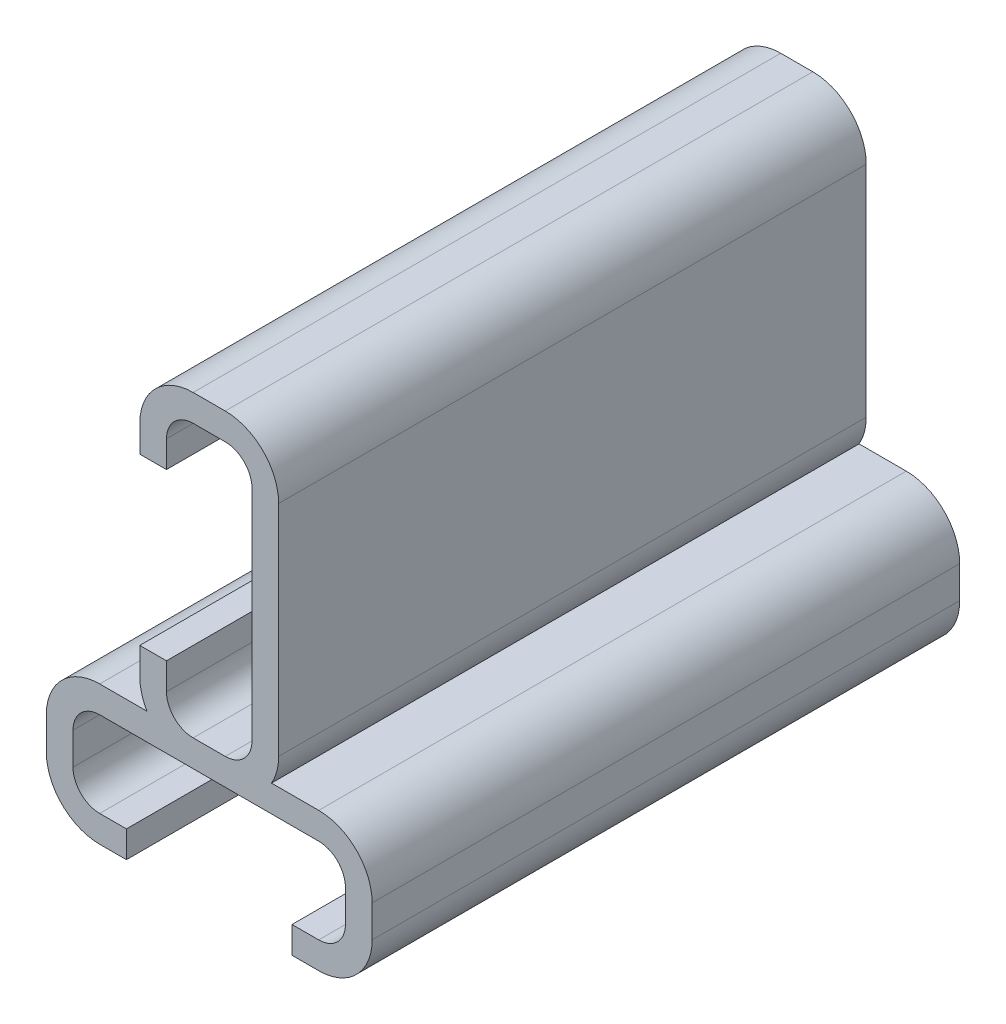
SolidWorks part; units mm, degrees
ref_plane "Plan de face" through (0, 0, 0) normal (0, 0, 1) x (1, 0, 0)
ref_plane "Plan de dessus" through (0, 0, 0) normal (0, 1, 0) x (1, 0, 0)
ref_plane "Plan de droite" through (0, 0, 0) normal (1, 0, 0) x (0, 0, -1)
sketch "Esquisse1" plane through (0, 0, 0) normal (0, 0, 1) x (1, 0, 0)
  line L1 (5.1, 0.6) -> (5.1, -0.6)
  line L2 (4.1, -1.6) -> (-4.1, -1.6)
  line L3 (-5.1, -0.6) -> (-5.1, 0.6)
  line L5 (6.1, 0.6) -> (6.1, -0.6)
  line L6 (4.1, -2.6) -> (-4.1, -2.6)
  line L7 (-6.1, -0.6) -> (-6.1, 0.6)
  line L8 (2.6, 3.6) -> (2.6, 11.8)
  line L9 (-0.6, 2.6) -> (0.6, 2.6)
  line L10 (-1.6, 3.6) -> (-1.6, 11.8)
  line L11 (-0.6, 12.8) -> (0.6, 12.8)
  line L12 (1.6, 3.6) -> (1.6, 11.8)
  line L13 (-0.6, 13.8) -> (0.6, 13.8)
  line L14 (-2.6, 3.6) -> (-2.6, 11.8)
  line L16 (-4.1, 2.6) -> (4.1, 2.6) construction
  line L17 (4.1, 2.6) -> (2.3321, 2.6)
  line L18 (-4.1, 2.6) -> (-2.3321, 2.6)
  line L19 (-4.1, 1.6) -> (4.1, 1.6)
  line L20 (-4.1, 1.6) -> (4.1, 1.6) construction
  line L21 (-0.6, 1.6) -> (0.6, 1.6) construction
  arc A0 (-4.1, -1.6) -> (-5.1, -0.6) centre (-4.1, -0.6) cw
  arc A1 (5.1, -0.6) -> (4.1, -1.6) centre (4.1, -0.6) cw
  arc A2 (4.1, 1.6) -> (5.1, 0.6) centre (4.1, 0.6) cw
  arc A3 (-4.1, 1.6) -> (-5.1, 0.6) centre (-4.1, 0.6) ccw
  arc A4 (4.1, 2.6) -> (6.1, 0.6) centre (4.1, 0.6) cw
  arc A5 (6.1, -0.6) -> (4.1, -2.6) centre (4.1, -0.6) cw
  arc A6 (-4.1, -2.6) -> (-6.1, -0.6) centre (-4.1, -0.6) cw
  arc A7 (-4.1, 2.6) -> (-6.1, 0.6) centre (-4.1, 0.6) ccw
  arc A8 (0.6, 2.6) -> (1.6, 3.6) centre (0.6, 3.6) ccw
  arc A9 (-0.6, 2.6) -> (-1.6, 3.6) centre (-0.6, 3.6) cw
  arc A10 (-1.6, 11.8) -> (-0.6, 12.8) centre (-0.6, 11.8) cw
  arc A11 (0.6, 12.8) -> (1.6, 11.8) centre (0.6, 11.8) cw
  arc A12 (0.6, 13.8) -> (2.6, 11.8) centre (0.6, 11.8) cw
  arc A13 (-2.6, 11.8) -> (-0.6, 13.8) centre (-0.6, 11.8) cw
  arc A14 (-0.6, 1.6) -> (-2.6, 3.6) centre (-0.6, 3.6) cw construction
  arc A15 (0.6, 1.6) -> (2.6, 3.6) centre (0.6, 3.6) ccw construction
  arc A16 (2.6, 3.6) -> (2.3321, 2.6) centre (0.6, 3.6) cw
  arc A17 (-2.6, 3.6) -> (-2.3321, 2.6) centre (-0.6, 3.6) ccw
  point P6 (-5.1, -1.6)
  point P11 (5.1, 1.6)
  point P14 (-5.1, 1.6)
  point P15 (0, 1.6)
  point P16 (-5.1, 0)
  point P37 (1.6, 2.6)
  point P40 (-1.6, 2.6)
  point P43 (-1.6, 12.8)
  point P46 (1.6, 12.8)
  point P63 (0, 2.6)
  dimension "D3" = 1
  dimension "D7" = 1
  dimension "D1" = 3.2
  dimension "D2" = 10.2
  dimension "D5" = 3.2
  dimension "D6" = 10.2
  dimension "D9" = 3.2
  dimension "D4" = 1
  dimension "D8" = 1
extrude "Boss.-Extru.2" add sketch "Esquisse1" along normal blind 10 contours L17 A16 L8 A12 L13 A13 L14 A17 L18 A7 L7 A6 L6 A5 L5 A4 | L10 A10 L11 A11 L12 A8 L9 A9 | L19 A2 L1 A1 L2 A0 L3 A3
sketch "Esquisse7" plane through (0, 0, 0) normal (0, 0, -1) x (-1, 0, 0)
  line L8 (-6.1, 0.6) -> (-6.1, -0.6)
  line L9 (-4.1, -2.6) -> (4.1, -2.6)
  line L10 (6.1, -0.6) -> (6.1, 0.6)
  line L11 (4.1, 2.6) -> (2.3321, 2.6)
  line L12 (2.6, 3.6) -> (2.6, 11.8)
  line L13 (0.6, 13.8) -> (-0.6, 13.8)
  line L14 (-2.6, 11.8) -> (-2.6, 3.6)
  line L15 (-2.3321, 2.6) -> (-4.1, 2.6)
  line L16 (-6.1, 0.6) -> (-6.1, -0.6)
  line L17 (-4.1, -2.6) -> (4.1, -2.6)
  line L18 (6.1, -0.6) -> (6.1, 0.6)
  line L19 (4.1, 2.6) -> (2.3321, 2.6)
  line L20 (2.6, 3.6) -> (2.6, 11.8)
  line L21 (0.6, 13.8) -> (-0.6, 13.8)
  line L22 (-2.6, 11.8) -> (-2.6, 3.6)
  line L23 (-2.3321, 2.6) -> (-4.1, 2.6)
  arc A8 (-4.1, 2.6) -> (-6.1, 0.6) centre (-4.1, 0.6) ccw
  arc A9 (-6.1, -0.6) -> (-4.1, -2.6) centre (-4.1, -0.6) ccw
  arc A10 (4.1, -2.6) -> (6.1, -0.6) centre (4.1, -0.6) ccw
  arc A11 (6.1, 0.6) -> (4.1, 2.6) centre (4.1, 0.6) ccw
  arc A12 (2.3321, 2.6) -> (2.6, 3.6) centre (0.6, 3.6) ccw
  arc A13 (2.6, 11.8) -> (0.6, 13.8) centre (0.6, 11.8) ccw
  arc A14 (-0.6, 13.8) -> (-2.6, 11.8) centre (-0.6, 11.8) ccw
  arc A15 (-2.6, 3.6) -> (-2.3321, 2.6) centre (-0.6, 3.6) ccw
  arc A16 (-4.1, 2.6) -> (-6.1, 0.6) centre (-4.1, 0.6) ccw
  arc A17 (-6.1, -0.6) -> (-4.1, -2.6) centre (-4.1, -0.6) ccw
  arc A18 (4.1, -2.6) -> (6.1, -0.6) centre (4.1, -0.6) ccw
  arc A19 (6.1, 0.6) -> (4.1, 2.6) centre (4.1, 0.6) ccw
  arc A20 (2.3321, 2.6) -> (2.6, 3.6) centre (0.6, 3.6) ccw
  arc A21 (2.6, 11.8) -> (0.6, 13.8) centre (0.6, 11.8) ccw
  arc A22 (-0.6, 13.8) -> (-2.6, 11.8) centre (-0.6, 11.8) ccw
  arc A23 (-2.6, 3.6) -> (-2.3321, 2.6) centre (-0.6, 3.6) ccw
  dimension "D1" = 0
extrude "Boss.-Extru.4" add sketch "Esquisse7" along normal blind 1
mirror "Symétrie1" about plane through (4.1, 0.6, -1) normal (0, 0, -1) of "Boss.-Extru.4", "Boss.-Extru.2"
sketch "Esquisse5" plane through (0, -2.6, 0) normal (0, -1, 0) x (1, 0, 0)
  line L0 (4.1, -12) -> (-4.1, -12) construction
  line L1 (3.1, -12) -> (-3.1, -12)
  line L2 (3.1, -12) -> (3.1, -2)
  line L3 (3.1, -2) -> (-3.1, -2)
  line L4 (-3.1, -12) -> (-3.1, -2)
  line L5 (4.1, 10) -> (-4.1, 10) construction
  line L6 (-3.1, 10) -> (3.1, 10)
  line L7 (-3.1, 10) -> (-3.1, 0)
  line L8 (-3.1, 0) -> (3.1, 0)
  line L9 (3.1, 10) -> (3.1, 0)
  line L10 (-4.1, 10) -> (-4.1, -12) construction
  line L11 (4.1, 10) -> (4.1, -12) construction
  dimension "D1" = 10
  dimension "D2" = 10
  dimension "D3" = 1
  dimension "D4" = 1
extrude "Enlèv. mat.-Extru.1" cut sketch "Esquisse5" against normal up to surface (1 mm away) up to face at (0, -1.6, -7)
sketch "Esquisse6" plane through (-2.6, 0, 0) normal (1, 0, 0) x (0, 0, -1)
  line L0 (12, 3.6) -> (12, 11.8) construction
  line L1 (12, 10.8) -> (2, 10.8)
  line L2 (12, 10.8) -> (12, 4.6)
  line L3 (12, 4.6) -> (2, 4.6)
  line L4 (2, 10.8) -> (2, 4.6)
  line L5 (-10, 3.6) -> (-10, 11.8) construction
  line L6 (-10, 10.8) -> (0, 10.8)
  line L7 (-10, 10.8) -> (-10, 4.6)
  line L8 (-10, 4.6) -> (0, 4.6)
  line L9 (0, 10.8) -> (0, 4.6)
  line L10 (-10, 11.8) -> (12, 11.8) construction
  line L11 (-10, 3.6) -> (12, 3.6) construction
  dimension "D1" = 10
  dimension "D2" = 10
  dimension "D3" = 1
  dimension "D4" = 1
extrude "Enlèv. mat.-Extru.2" cut sketch "Esquisse6" against normal up to surface (4.2 mm away)
